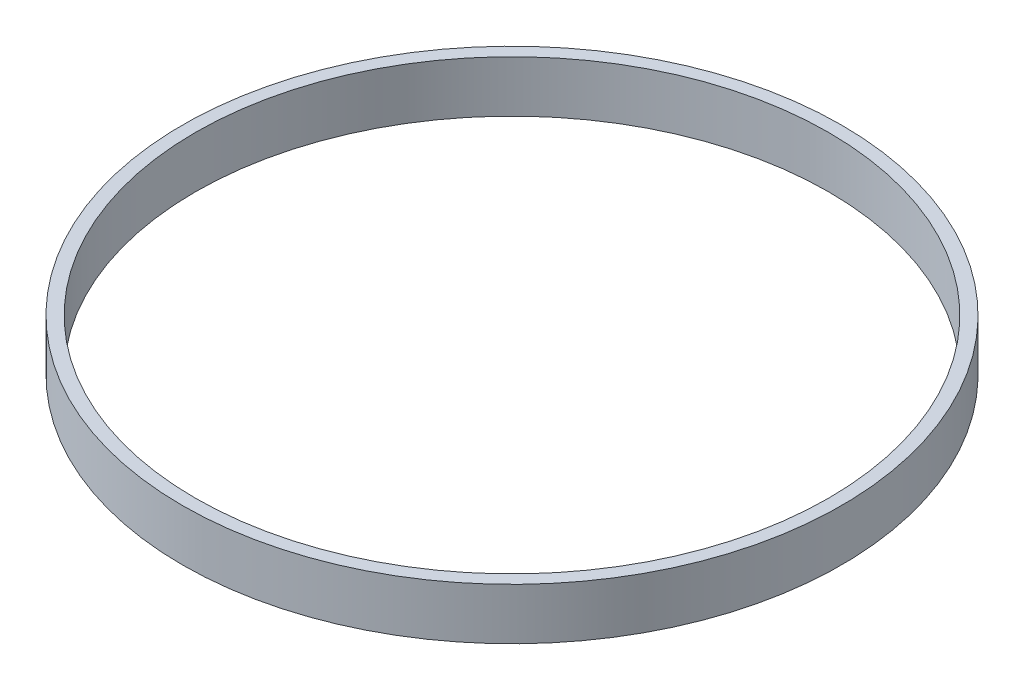
SolidWorks part; units mm, degrees
material "AISI 304"
ref_plane "Front Plane" through (0, 0, 0) normal (0, 0, 1) x (1, 0, 0)
ref_plane "Top Plane" through (0, 0, 0) normal (0, 1, 0) x (1, 0, 0)
ref_plane "Right Plane" through (0, 0, 0) normal (1, 0, 0) x (0, 0, -1)
sketch "Sketch1" plane through (0, 0, 0) normal (0, 1, 0) x (1, 0, 0)
  circle A0 centre (0, 0) radius 78.1558
  circle A1 centre (0, 0) radius 81.3308
  dimension "D1" = 156.3116
  dimension "D2" = 3.175
extrude "Boss-Extrude1" add sketch "Sketch1" along normal blind 12.7
equation "\"D2@Sketch1\"=\"shroud thickness@[TP] [Turb] Turbine.Assembly\""
equation "\"D1@Sketch1\"=2*\"rotor tip@[TP] [Turb] Turbine.Assembly\""
